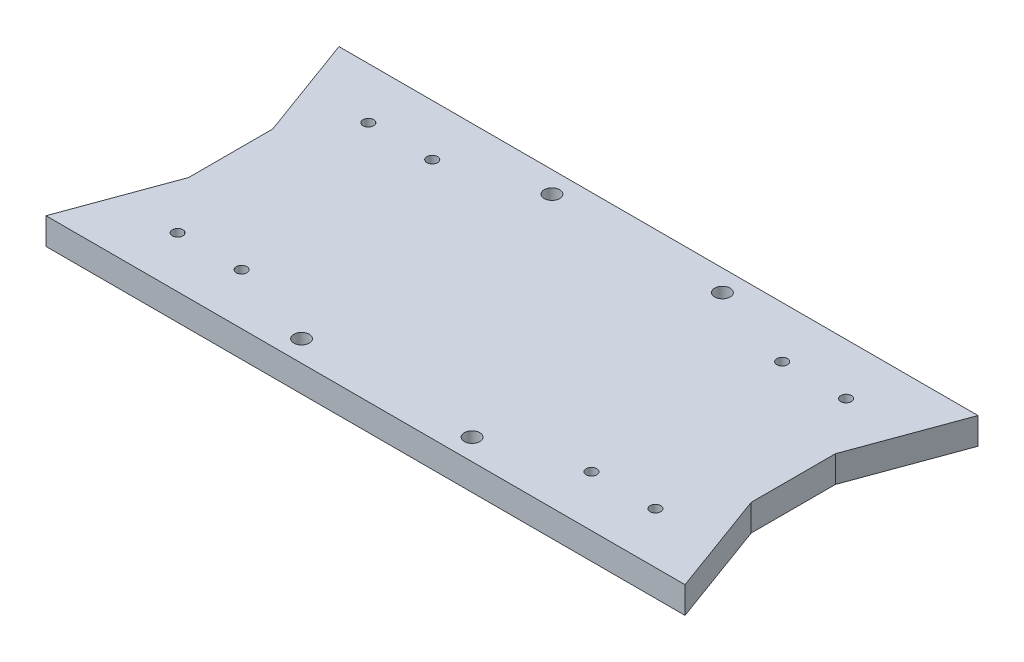
SolidWorks part; units mm, degrees
ref_plane "Front Plane" through (0, 0, 0) normal (0, 0, 1) x (1, 0, 0)
ref_plane "Top Plane" through (0, 0, 0) normal (0, 1, 0) x (1, 0, 0)
ref_plane "Right Plane" through (0, 0, 0) normal (1, 0, 0) x (0, 0, -1)
sketch "Sketch1" plane through (0, 0, 0) normal (0, 1, 0) x (1, 0, 0)
  line L0 (28.7276, 102.6327) -> (-38.3337, 102.6327) construction
  line L1 (-38.3337, 32.7827) -> (28.7276, 32.7827)
  line L2 (-38.3337, 32.7827) -> (-38.3337, 102.6327)
  line L3 (-38.3337, 102.6327) -> (28.7276, 102.6327)
  line L4 (28.7276, 32.7827) -> (28.7276, 102.6327)
  line L5 (-38.3337, 32.7827) -> (28.7276, 32.7827) construction
  line L6 (-38.3337, 102.6327) -> (-38.3337, 32.7827) construction
  circle A1 centre (3.3813, 90.4077) radius 1.27
  circle A2 centre (18.6213, 90.4077) radius 1.27
  circle A3 centre (3.3813, 44.9477) radius 1.27
  circle A4 centre (18.6213, 44.9477) radius 1.27
  dimension "D5" = 2.54
  dimension "D6" = 2.54
  dimension "D7" = 2.54
  dimension "D8" = 2.54
  dimension "D1" = 0
  dimension "D2" = 0
  dimension "D3" = 0
  dimension "D4" = 0
extrude "Boss-Extrude1" add sketch "Sketch1" along normal blind 6.35
sketch "Sketch2" plane through (0, 6.35, 0) normal (0, 1, 0) x (1, 0, 0)
  line L1 (28.7276, 57.6777) -> (7.7513, 57.6777)
  line L2 (28.7276, 57.6777) -> (28.7276, 77.7377)
  line L3 (28.7276, 77.7377) -> (7.7513, 77.7377)
  line L4 (7.7513, 57.6777) -> (7.7513, 77.7377)
extrude "Boss-Extrude2" add sketch "Sketch2" along normal blind 12.7
sketch "Sketch3" plane through (0, 6.35, 0) normal (0, 1, 0) x (1, 0, 0)
  line L1 (37.8413, 102.6327) -> (28.7276, 77.7377)
  line L2 (28.7276, 77.7377) -> (28.7276, 102.6327)
  line L3 (28.7276, 102.6327) -> (37.8413, 102.6327)
  line L4 (28.7276, 57.6777) -> (37.8413, 32.7827)
  line L5 (37.8413, 32.7827) -> (28.7276, 32.7827)
  line L6 (28.7276, 32.7827) -> (28.7276, 57.6777)
extrude "Boss-Extrude3" add sketch "Sketch3" against normal blind 6.35
mirror "Mirror2" about plane through (-38.3337, 6.35, -32.7827) normal (1, 0, 0) of "Boss-Extrude1", "Boss-Extrude2", "Boss-Extrude3"
sketch "Sketch4" plane through (0, 0, -32.7827) normal (0, 0, 1) x (1, 0, 0)
  line L1 (37.8413, 6.35) -> (-133.1569, 6.35)
  line L2 (37.8413, 6.35) -> (37.8413, 24.3471)
  line L3 (37.8413, 24.3471) -> (-133.1569, 24.3471)
  line L4 (-133.1569, 6.35) -> (-133.1569, 24.3471)
extrude "Cut-Extrude1" cut sketch "Sketch4" against normal through all
sketch "Sketch5" plane through (0, 0, 0) normal (0, -1, 0) x (1, 0, 0)
  circle A1 centre (21.0248, -94.445) radius 0.1639
sketch "Sketch6" plane through (0, 0, 0) normal (0, -1, 0) x (-1, 0, 0)
  circle A0 centre (-37.8413, 67.7077) radius 31.75
  dimension "D1" = 63.5
sketch "Sketch7" plane through (0, 6.35, 0) normal (0, 1, 0) x (1, 0, 0)
  circle A0 centre (3.3813, 90.4077) radius 1.2687
  circle A1 centre (18.6213, 90.4077) radius 1.2687
  circle A2 centre (3.3813, 44.9477) radius 1.2687
  circle A4 centre (18.6213, 44.9477) radius 1.2687
  dimension "D1" = 2.5375
  dimension "D2" = 2.5375
  dimension "D3" = 2.5375
  dimension "D4" = 2.5375
sketch "Sketch8" plane through (0, 6.35, 0) normal (0, 1, 0) x (1, 0, 0)
  line L0 (37.8413, 102.6327) -> (-114.5087, 102.6327) construction
  line L1 (-23.0937, 188.9927) -> (-23.0937, 92.4727) construction
  line L2 (-53.5737, 188.9927) -> (-53.5737, 92.4727) construction
  line L3 (-114.5087, 32.7827) -> (37.8413, 32.7827) construction
  circle A0 centre (-58.6537, 97.5527) radius 1.8415
  circle A1 centre (-18.0137, 97.5527) radius 1.8415
  circle A2 centre (-18.0137, 37.8627) radius 1.8415
  circle A3 centre (-58.6537, 37.8627) radius 1.8415
  dimension "D1" = 3.683
  dimension "D2" = 3.683
  dimension "D3" = 3.683
  dimension "D4" = 3.683
  dimension "D5" = 5.08
  dimension "D6" = 5.08
  dimension "D7" = 5.08
  dimension "D8" = 5.08
  dimension "D9" = 5.08
  dimension "D10" = 5.08
extrude "Cut-Extrude3" cut sketch "Sketch8" against normal blind 13.716
